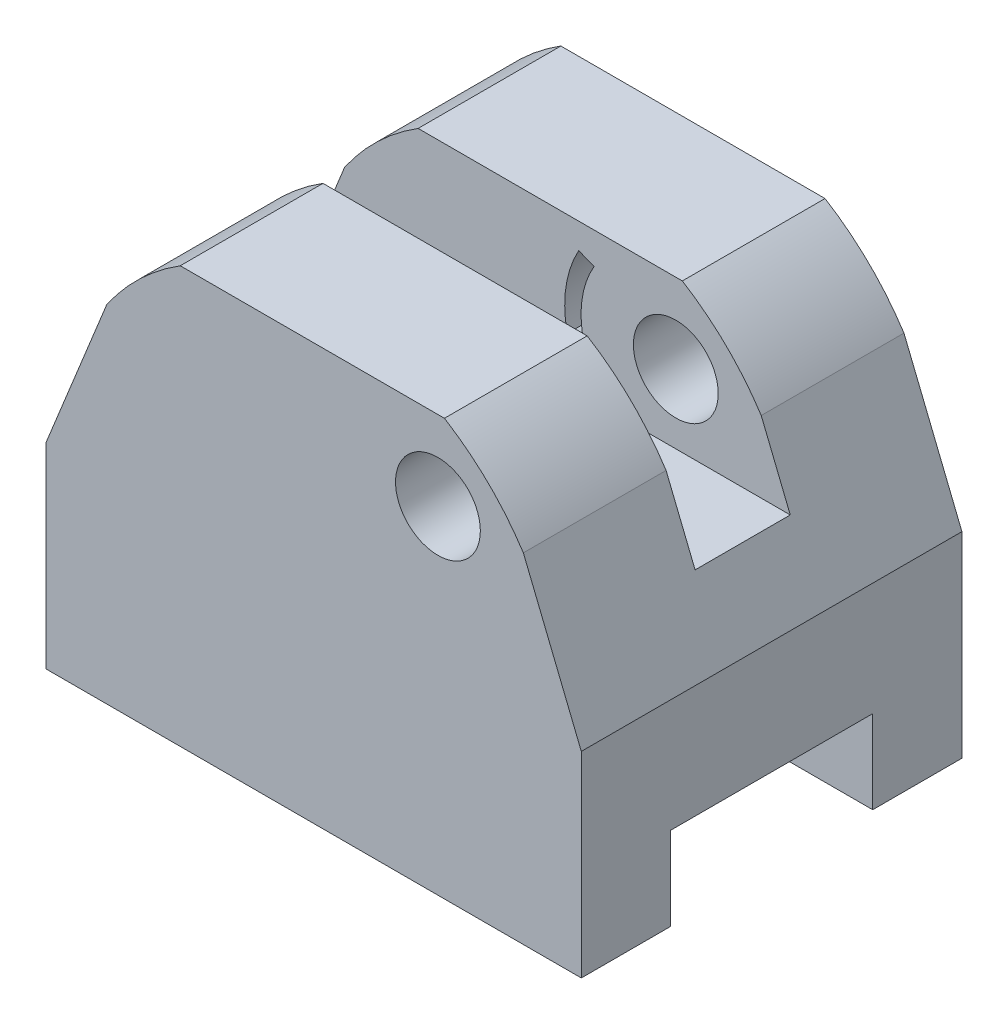
SolidWorks part; units mm, degrees
ref_plane "Front" through (0, 0, 0) normal (0, 0, 1) x (1, 0, 0)
ref_plane "Top" through (0, 0, 0) normal (0, 1, 0) x (1, 0, 0)
ref_plane "Right" through (0, 0, 0) normal (1, 0, 0) x (0, 0, -1)
sketch "Sketch1" plane through (0, 0, 0) normal (1, 0, 0) x (0, 0, -1)
  line L9 (-32, -16.5) -> (32, -16.5)
  line L10 (-32, -16.5) -> (-32, 16.5)
  line L11 (-32, 16.5) -> (32, 16.5)
  line L12 (32, -16.5) -> (32, 16.5)
  line L13 (-32, -16.5) -> (32, 16.5) construction
  line L14 (-32, 16.5) -> (32, -16.5) construction
  point P0 (0, 0)
  dimension "D1" = 64
  dimension "D2" = 33
extrude "Boss-Extrude2" add sketch "Sketch1" along normal blind 90
sketch "Sketch5" plane through (0, 0, 0) normal (-1, 0, 0) x (0, 0, 1)
  line L0 (32, -16.5) -> (-32, -16.5) construction
  line L1 (-17, -16.5) -> (17, -16.5)
  line L2 (-17, -16.5) -> (-17, -2.5)
  line L3 (-17, -2.5) -> (17, -2.5)
  line L4 (17, -16.5) -> (17, -2.5)
  line L5 (32, 16.5) -> (32, -16.5) construction
  dimension "D1" = 15
  dimension "D2" = 14
  dimension "D3" = 34
extrude "Cut-Extrude1" cut sketch "Sketch5" against normal through all contours L3 L4 L1 L2
sketch "Sketch7" plane through (0, 16.5, 0) normal (0, 1, 0) x (1, 0, 0)
  line L1 (0, -32) -> (90, -32)
  line L2 (0, -32) -> (0, 32)
  line L3 (0, 32) -> (90, 32)
  line L4 (90, -32) -> (90, 32)
  line L5 (0, -32) -> (90, 32) construction
  line L6 (0, 32) -> (90, -32) construction
  point P0 (45, 0)
  dimension "D1" = 64
  dimension "D2" = 90
extrude "Boss-Extrude3" add sketch "Sketch7" along normal blind 37
sketch "Sketch9" plane through (0, 0, 0) normal (-1, 0, 0) x (0, 0, 1)
  line L1 (-32, 53.5) -> (32, 53.5) construction
  line L4 (-8, 53.5) -> (8, 53.5)
  line L5 (-8, 53.5) -> (-8, 28.5)
  line L6 (-8, 28.5) -> (8, 28.5)
  line L7 (8, 28.5) -> (8, 53.5)
  line L12 (0, 28.5) -> (0, -2.5) construction
  line L13 (-17, -2.5) -> (17, -2.5) construction
  dimension "D1" = 25
  dimension "D3" = 16
extrude "Cut-Extrude2" cut sketch "Sketch9" against normal through all
sketch "Sketch10" plane through (0, 0, 32) normal (0, 0, 1) x (1, 0, 0)
  line L0 (0, 16.5) -> (15, 53.5)
  line L1 (0, 53.5) -> (0, -16.5) construction
  line L2 (0, 53.5) -> (90, 53.5) construction
  line L3 (15, 53.5) -> (0, 53.5)
  line L4 (0, 53.5) -> (0, 16.5)
  line L5 (90, -16.5) -> (0, -16.5) construction
  line L6 (45, 53.5) -> (45, 24.836) construction
  line L7 (90, 53.5) -> (90, 16.5)
  line L8 (90, 16.5) -> (75, 53.5)
  line L9 (75, 53.5) -> (90, 53.5)
  dimension "D1" = 33
  dimension "D2" = 60
extrude "Cut-Extrude3" cut sketch "Sketch10" against normal through all
sketch "Sketch11" plane through (0, 0, 32) normal (0, 0, 1) x (1, 0, 0)
  line L0 (45, 53.5) -> (45, -18.0757) construction
  line L1 (15, 53.5) -> (75, 53.5) construction
  line L2 (45, 17.7122) -> (94.4478, 17.7122) construction
  line L3 (94.4478, 17.7122) -> (-3.6629, 17.7122) construction
  line L4 (0, 16.5) -> (15, 53.5) construction
  line L5 (75, 53.5) -> (90, 16.5) construction
  line L6 (22.5593, 53.5) -> (15, 53.5)
  line L7 (15, 53.5) -> (10.1962, 41.6507)
  line L8 (80.2529, 40.543) -> (75, 53.5)
  line L9 (75, 53.5) -> (66.9827, 53.5)
  arc A0 (10.1962, 41.6507) -> (22.5593, 53.5) centre (45, 17.7122) cw
  arc A1 (80.2529, 40.543) -> (66.9827, 53.5) centre (45, 17.7122) ccw
  dimension "D4" = 23.39
  dimension "D5" = 42.2416
  dimension "D6" = 25.511
  dimension "D7" = 42.0001
  dimension "D1" = 71.5757
  dimension "D2" = 49.4478
  dimension "D3" = 98.1107
  dimension "D8" = 7.5593
  dimension "D9" = 12.786
  dimension "D10" = 13.9813
  dimension "D11" = 8.0173
extrude "Cut-Extrude4" cut sketch "Sketch11" against normal through all
sketch "Sketch12" plane through (0, 0, -32) normal (0, 0, -1) x (-1, 0, 0)
  line L0 (-44.771, 53.5) -> (-45, -16.5) construction
  line L3 (-66.9827, 53.5) -> (-22.5593, 53.5) construction
  line L4 (-90, -16.5) -> (0, -16.5) construction
  line L5 (-44.8855, 18.5) -> (-90.0524, 18.5) construction
  circle A0 centre (-65.8903, 40.1233) radius 4.5633
  dimension "D3" = 4.5633
  dimension "D1" = 70.0004
  dimension "D2" = 45.1669
extrude "Cut-Extrude5" cut sketch "Sketch12" against normal through all
sketch "Sketch13" plane through (0, 28.5, 0) normal (0, 1, 0) x (1, 0, 0)
  circle A0 centre (18.5598, 1.3033) radius 3.3962
  dimension "D1" = 3.3962
extrude "Cut-Extrude7" cut sketch "Sketch13" against normal blind 4
sketch "Sketch14" plane through (0, 0, 32) normal (0, 0, 1) x (1, 0, 0)
  circle A0 centre (65.8903, 40.1233) radius 7.1318
  dimension "D1" = 7.1318
extrude "Cut-Extrude8" cut sketch "Sketch14" against normal through all
sketch "Sketch15" plane through (0, 0, 32) normal (0, 0, 1) x (1, 0, 0)
  line L0 (66.9827, 53.5) -> (66.9827, 13.7829) construction
  line L1 (65.8903, 40.1233) -> (31.006, 40.1233) construction
  line L2 (52.1442, 48.1786) -> (49.5681, 49.2129)
  line L3 (50.191, 37.4076) -> (47.6308, 36.1702)
  arc A0 (49.5681, 49.2129) -> (47.6308, 36.1702) centre (65.8903, 40.1233) ccw
  arc A1 (52.1442, 48.1786) -> (50.191, 37.4076) centre (65.8903, 40.1233) ccw
  dimension "D3" = 41.328
  dimension "D4" = 18.6825
  dimension "D5" = 40.185
  dimension "D6" = 15.9324
  dimension "D7" = 2.776
  dimension "D1" = 39.7171
  dimension "D2" = 34.8843
  dimension "D8" = 2.8436
extrude "Cut-Extrude9" cut sketch "Sketch15" against normal blind 30 from offset 17
